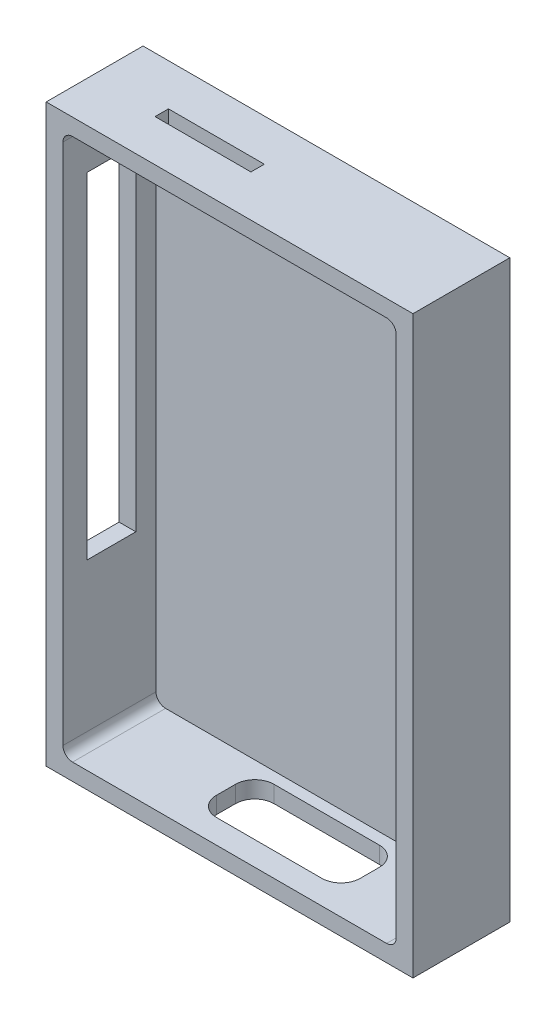
SolidWorks part; units mm, degrees
ref_plane "正面" through (0, 0, 0) normal (0, 0, 1) x (1, 0, 0)
ref_plane "平面" through (0, 0, 0) normal (0, 1, 0) x (1, 0, 0)
ref_plane "右側面" through (0, 0, 0) normal (1, 0, 0) x (0, 0, -1)
sketch "ｽｹｯﾁ1" plane through (0, 0, 0) normal (0, 0, 1) x (1, 0, 0)
  line L1 (0, 0) -> (76.5, 0)
  line L2 (0, 0) -> (0, 120)
  line L3 (0, 120) -> (76.5, 120)
  line L4 (76.5, 0) -> (76.5, 120)
  dimension "D1" = 76.5
  dimension "D2" = 120
extrude "ﾎﾞｽ - 押し出し1" add sketch "ｽｹｯﾁ1" along normal blind 0.8
sketch "ｽｹｯﾁ10" plane through (0, 0, 0.8) normal (0, 0, 1) x (1, 0, 0)
  line L0 (0, 120) -> (0, 0) construction
  line L5 (73, 3.5) -> (3.5, 3.5)
  line L6 (73, 3.5) -> (73, 116.5)
  line L7 (73, 116.5) -> (3.5, 116.5)
  line L8 (3.5, 3.5) -> (3.5, 116.5)
  line L9 (0, 0) -> (76.5, 0) construction
  line L10 (76.5, 0) -> (76.5, 120) construction
  line L11 (76.5, 120) -> (0, 120) construction
  line L17 (0, 120) -> (76.5, 120)
  line L18 (0, 120) -> (0, 0)
  line L19 (0, 0) -> (76.5, 0)
  line L20 (76.5, 120) -> (76.5, 0)
  dimension "D1" = 3.5
  dimension "D2" = 3.5
  dimension "D3" = 3.5
  dimension "D4" = 3.5
extrude "ﾎﾞｽ - 押し出し2" add sketch "ｽｹｯﾁ10" along normal blind 19.4
fillet "ﾌｨﾚｯﾄ1" radius 2 4 edges at (73, 116.5, 10.5) (73, 3.5, 10.5) (3.5, 3.5, 10.5) (3.5, 116.5, 10.5)
sketch "ｽｹｯﾁ11" plane through (0, 0, 0) normal (-1, 0, 0) x (0, 0, 1)
  line L0 (0, 120) -> (0, 0) construction
  line L5 (5, 106.5) -> (15.2, 106.5)
  line L6 (5, 106.5) -> (5, 36.5)
  line L7 (5, 36.5) -> (15.2, 36.5)
  line L8 (15.2, 106.5) -> (15.2, 36.5)
  line L9 (20.2, 120) -> (20.2, 0) construction
  line L10 (20.2, 120) -> (0, 120) construction
  dimension "D1" = 5
  dimension "D2" = 5
  dimension "D3" = 13.5
  dimension "D4" = 70
extrude "ｶｯﾄ - 押し出し1" cut sketch "ｽｹｯﾁ11" against normal up to surface (3.5 mm away) up to face at (3.5, 60, 10.5)
sketch "ｽｹｯﾁ12" plane through (0, 0, 0) normal (0, -1, 0) x (-1, 0, 0)
  line L0 (0, -20.2) -> (-76.5, -20.2) construction
  line L1 (-56.5, -15.2) -> (-26.5, -15.2)
  line L2 (-56.5, -15.2) -> (-56.5, -3.2)
  line L3 (-56.5, -3.2) -> (-26.5, -3.2)
  line L4 (-26.5, -15.2) -> (-26.5, -3.2)
  line L5 (-76.5, -20.2) -> (-76.5, 0) construction
  dimension "D1" = 12
  dimension "D2" = 30
  dimension "D3" = 5
  dimension "D4" = 20
extrude "ｶｯﾄ - 押し出し2" cut sketch "ｽｹｯﾁ12" against normal blind 10
fillet "ﾌｨﾚｯﾄ2" radius 4 4 edges at (26.5, 1.75, 15.2) (26.5, 1.75, 3.2) (56.5, 1.75, 15.2) (56.5, 1.75, 3.2)
sketch "ｽｹｯﾁ13" plane through (0, 120, 0) normal (0, 1, 0) x (1, 0, 0)
  line L0 (0, -10.1) -> (76.5, -10.1) construction
  line L1 (0, -20.2) -> (0, 0) construction
  line L2 (76.5, -20.2) -> (76.5, 0) construction
  line L3 (38.25, -19.745) -> (38.25, 0) construction
  line L4 (76.5, 0) -> (0, 0) construction
  line L6 (14, -11.5) -> (34, -11.5)
  line L7 (14, -11.5) -> (14, -8.7)
  line L8 (14, -8.7) -> (34, -8.7)
  line L9 (34, -11.5) -> (34, -8.7)
  line L10 (14, -11.5) -> (34, -8.7) construction
  line L11 (14, -8.7) -> (34, -11.5) construction
  point P10 (24, -10.1)
  dimension "D1" = 20
  dimension "D2" = 2.8
  dimension "D3" = 14
extrude "ｶｯﾄ - 押し出し3" cut sketch "ｽｹｯﾁ13" against normal up to next
ref_plane "この面でカットして3Dプリント" through (0, 0, 10.2) normal (0, 0, -1) x (-1, 0, 0)
sketch "ｽｹｯﾁ14" plane through (0, 0, 10.2) normal (0, 0, -1) x (-1, 0, 0)
  line L1 (0, 120) -> (-76.5, 120)
  line L2 (0, 120) -> (0, 0)
  line L3 (0, 0) -> (-76.5, 0)
  line L4 (-76.5, 120) -> (-76.5, 0)
extrude "ｶｯﾄ - 押し出し5" [suppressed] cut sketch "ｽｹｯﾁ14" against normal through all
